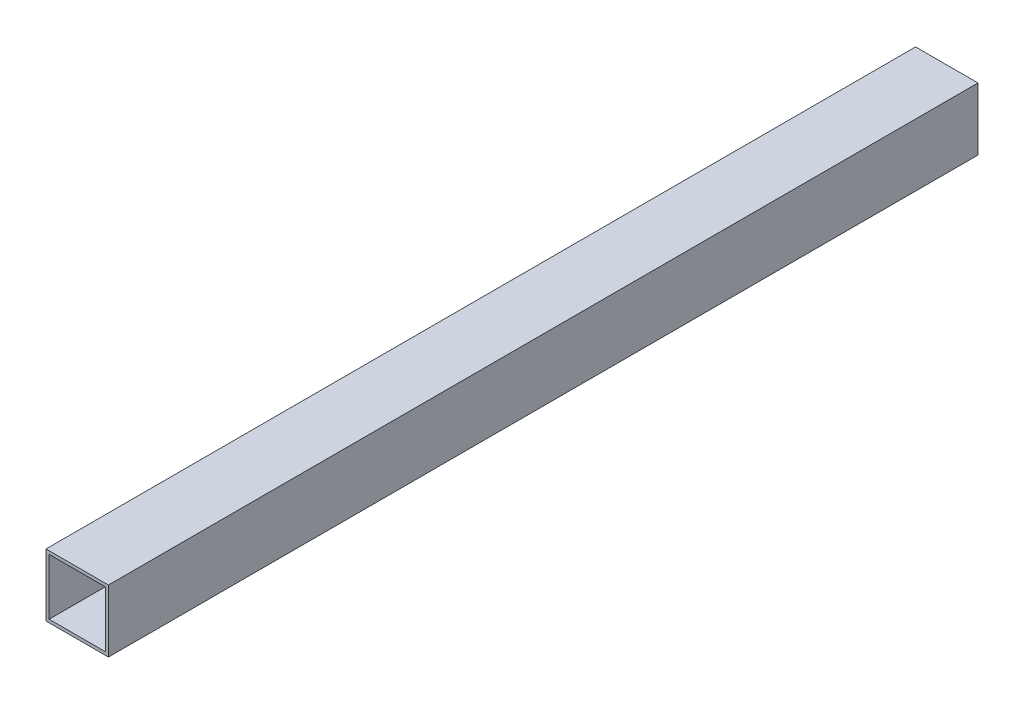
SolidWorks part; units mm, degrees
ref_plane "前视基准面" through (0, 0, 0) normal (0, 0, 1) x (1, 0, 0)
ref_plane "上视基准面" through (0, 0, 0) normal (0, 1, 0) x (1, 0, 0)
ref_plane "右视基准面" through (0, 0, 0) normal (1, 0, 0) x (0, 0, -1)
other "Configuration Table"
sketch "草图1" plane through (0, 0, 0) normal (0, 0, 1) x (1, 0, 0)
  line L0 (-9, 9) -> (9, 9)
  line L1 (-10, 10) -> (10, 10)
  line L2 (-10, 10) -> (-10, -10)
  line L3 (-10, -10) -> (10, -10)
  line L4 (10, 10) -> (10, -10)
  line L5 (-10, 10) -> (10, -10) construction
  line L6 (-10, -10) -> (10, 10) construction
  line L7 (9, 9) -> (9, -9)
  line L8 (-9, -9) -> (9, -9)
  line L9 (-9, 9) -> (-9, -9)
  point P0 (0, 0)
  dimension "D1" = 20
  dimension "D2" = 20
  dimension "D3" = 1
extrude "凸台-拉伸1" add sketch "草图1" along normal blind 278.56
